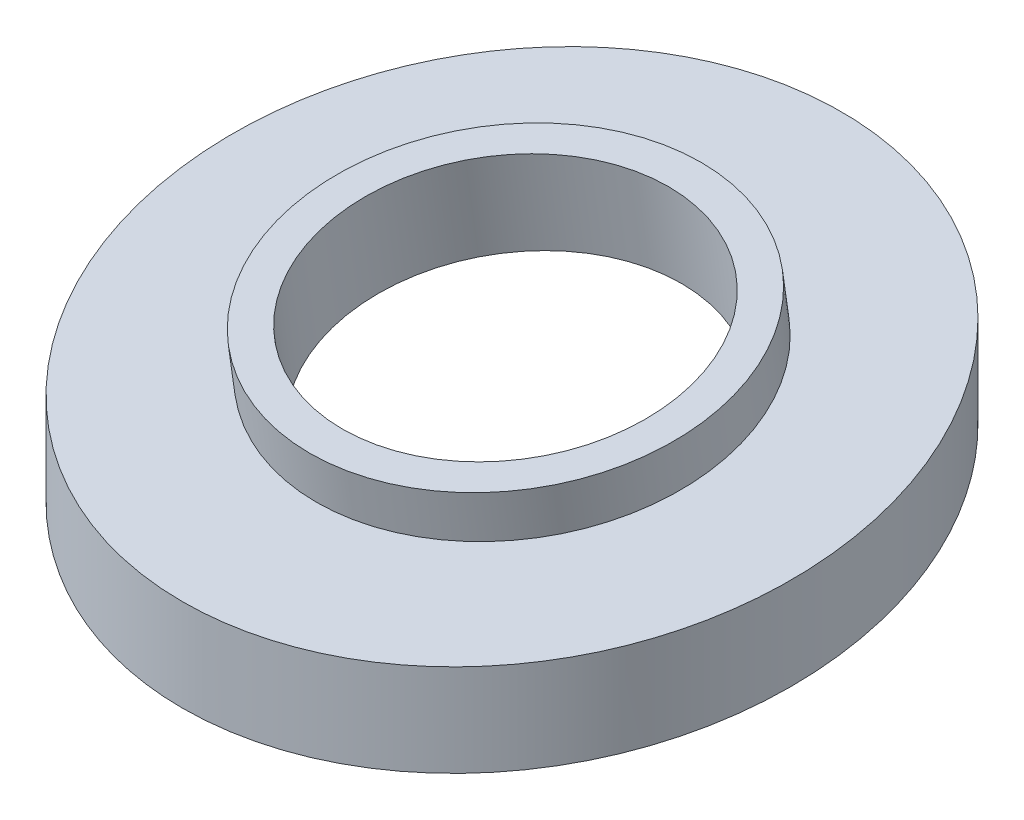
SolidWorks part; units mm, degrees
ref_plane "前视基准面" through (0, 0, 0) normal (0, 0, 1) x (1, 0, 0)
ref_plane "上视基准面" through (0, 0, 0) normal (0, 1, 0) x (1, 0, 0)
ref_plane "右视基准面" through (0, 0, 0) normal (1, 0, 0) x (0, 0, -1)
sketch "草图1" plane through (0, 0, 0) normal (0, 1, 0) x (1, 0, 0)
  circle A0 centre (0, 0) radius 25
  dimension "D1" = 50
extrude "凸台-拉伸1" add sketch "草图1" along normal blind 30
sketch "草图3" plane through (0, 0, 0) normal (1, 0, 0) x (0, 0, -1)
  line L0 (-25, 7) -> (25, 14.1889)
  line L1 (-25, 30) -> (-25, 0) construction
  line L2 (25, 0) -> (25, 30) construction
  line L3 (25, 14.1889) -> (25, 39.51)
  line L4 (25, 39.51) -> (-25, 39.51)
  line L5 (-25, 39.51) -> (-25, 7)
  line L6 (-25, 0) -> (25, 0) construction
  line L7 (0, 0) -> (0, 30.0856) construction
  line L12 (-25, 0) -> (25, 7.1889)
  line L13 (25, 0) -> (25, 30) construction
  line L14 (25, 7.1889) -> (25, -11.5725)
  line L15 (25, -11.5725) -> (-25, -11.5725)
  line L16 (-25, -11.5725) -> (-25, 0)
  line L17 (-20.2882, -2.8585) -> (21.2844, 3.1187) construction
  line L18 (-20.2882, -2.8585) -> (-21.2844, 4.0702) construction
  line L19 (21.2844, 3.1187) -> (20.2882, 10.0474) construction
  line L20 (-21.2844, 4.0702) -> (20.2882, 10.0474) construction
  line L21 (-20.2882, -2.8585) -> (20.2882, 10.0474) construction
  line L22 (21.2844, 3.1187) -> (-21.2844, 4.0702) construction
  point P21 (0, 3.5944)
  dimension "D1" = 7
  dimension "D2" = 8.182
  dimension "D3" = 42
  dimension "D4" = 0
  dimension "D5" = 7
  dimension "D6" = 3.4288
extrude "切除-拉伸1" cut sketch "草图3" against normal mid plane 63
sketch "草图10" plane through (0, 10.3799, 1.4924) normal (0, 0.9898, 0.1423) x (1, 0, 0)
  circle A0 centre (0, 1.5077) radius 15
  ellipse E0 centre (0, 1.5077) end of major axis (0, -23.7493) minor radius 25 construction
  dimension "D1" = 30
extrude "凸台-拉伸2" add sketch "草图10" along normal blind 3.5
sketch "草图11" plane through (0, 3.5216, 0.5063) normal (0, -0.9898, -0.1423) x (1, 0, 0)
  line L0 (-25, -0.5115) -> (25, -0.5115) construction
  circle A0 centre (0, -1.5077) radius 21
  circle A6 centre (0, -1.5077) radius 15 construction
  dimension "D1" = 42
  dimension "D2" = 0.9962
extrude "切除-拉伸8" cut sketch "草图11" against normal blind 3.5
sketch "草图12" plane through (0, 13.8443, 1.9905) normal (0, 0.9898, 0.1423) x (1, 0, 0)
  circle A2 centre (0, 1.5077) radius 12.5
  dimension "D1" = 25
extrude "切除-拉伸9" cut sketch "草图12" against normal blind 23.5
